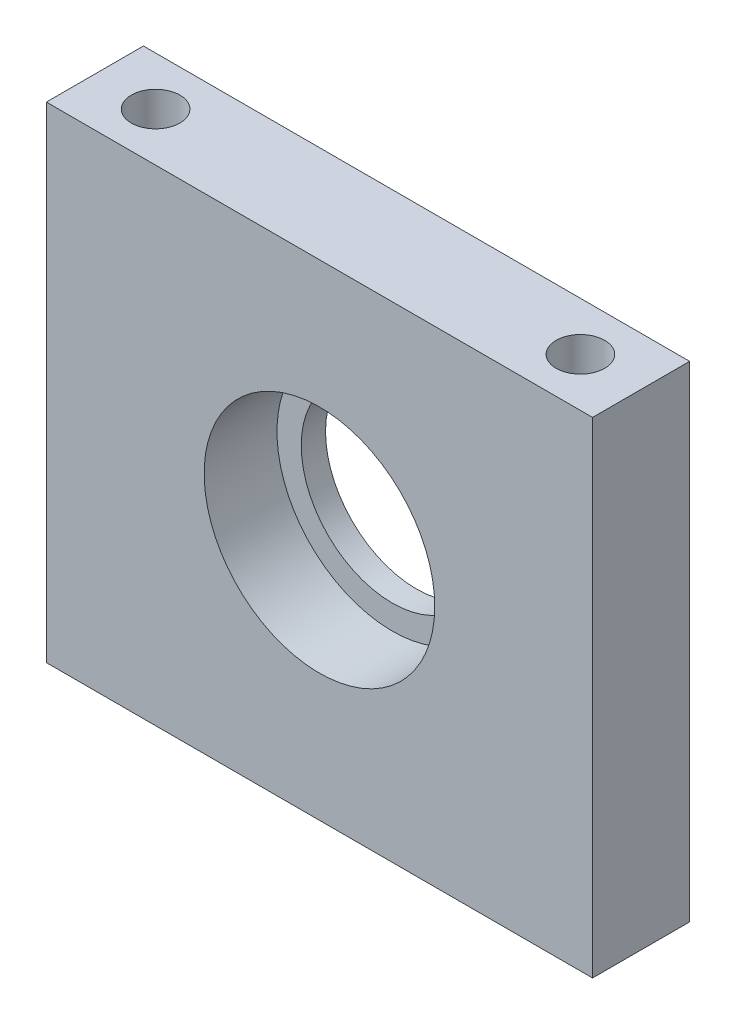
SolidWorks part; units mm, degrees
material "Alliage 1060"
ref_plane "Plan de face" through (0, 0, 0) normal (0, 0, 1) x (1, 0, 0)
ref_plane "Plan de dessus" through (0, 0, 0) normal (0, 1, 0) x (1, 0, 0)
ref_plane "Plan de droite" through (0, 0, 0) normal (1, 0, 0) x (0, 0, -1)
sketch "Esquisse1" plane through (0, 0, 0) normal (0, 0, 1) x (1, 0, 0)
  line L1 (-22.5, -20) -> (22.5, -20)
  line L2 (-22.5, -20) -> (-22.5, 20)
  line L3 (-22.5, 20) -> (22.5, 20)
  line L4 (22.5, -20) -> (22.5, 20)
  line L5 (-22.5, -20) -> (22.5, 20) construction
  line L6 (-22.5, 20) -> (22.5, -20) construction
  point P0 (0, 0)
  dimension "D1" = 45
  dimension "D2" = 40
extrude "Boss.-Extru.1" add sketch "Esquisse1" along normal blind 8
sketch "Esquisse2" plane through (0, 0, 8) normal (0, 0, 1) x (1, 0, 0)
  circle A0 centre (0, 0) radius 7.5
  dimension "D1" = 15
extrude "Enlèv. mat.-Extru.1" cut sketch "Esquisse2" against normal through all
sketch "Esquisse3" plane through (0, 0, 8) normal (0, 0, 1) x (1, 0, 0)
  circle A0 centre (0, 0) radius 9.5
  dimension "D1" = 19
extrude "Enlèv. mat.-Extru.2" cut sketch "Esquisse3" against normal blind 6
sketch "Esquisse4" plane through (0, 20, 0) normal (0, 1, 0) x (1, 0, 0)
  line L0 (22.5, 0) -> (-22.5, 0) construction
  line L1 (-22.5, -8) -> (-22.5, 0) construction
  line L2 (22.5, -8) -> (22.5, 0) construction
  circle A0 centre (-17.5, -4) radius 2
  circle A1 centre (17.5, -4) radius 2
  dimension "D1" = 4
  dimension "D2" = 4
  dimension "D4" = 5
  dimension "D5" = 4
  dimension "D6" = 5
  dimension "D3" = 4
extrude "Enlèv. mat.-Extru.3" cut sketch "Esquisse4" against normal through all
